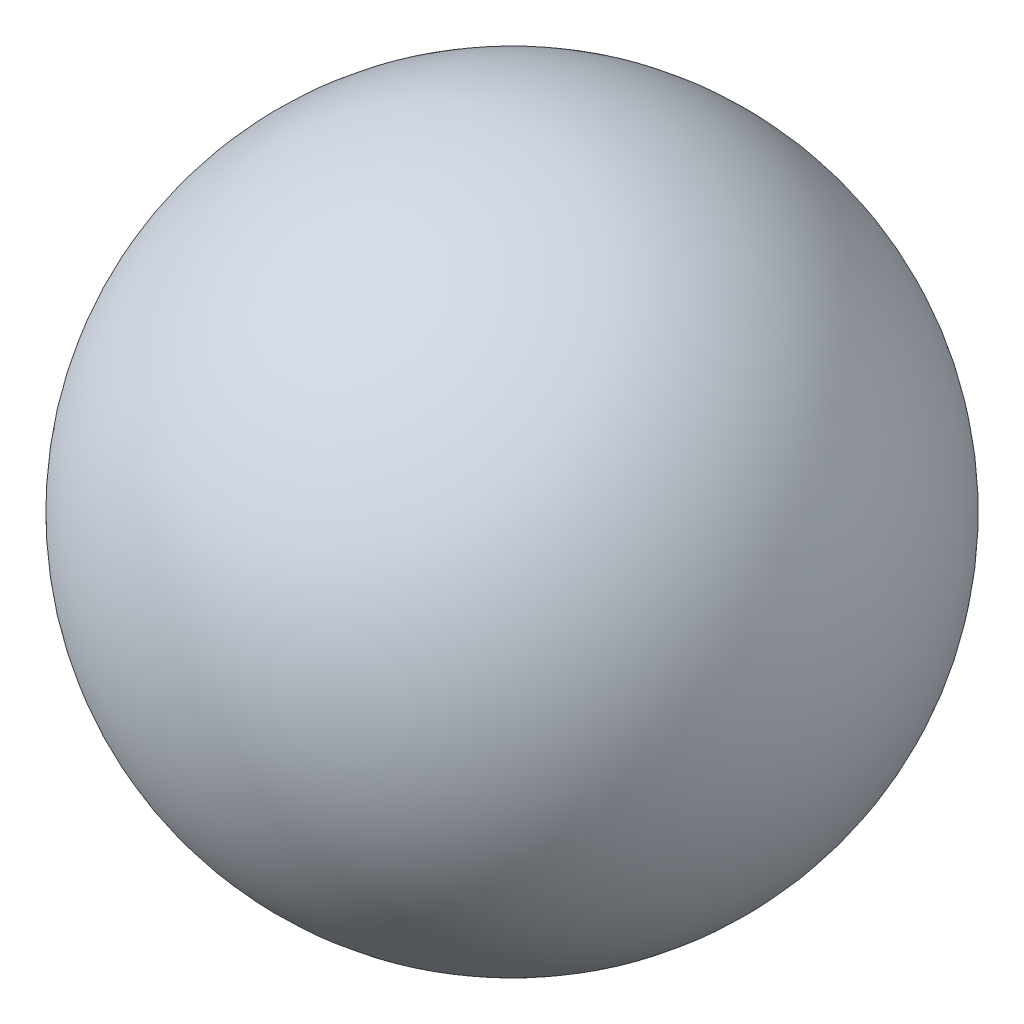
SolidWorks part; units mm, degrees
material "ABS"
ref_plane "Front Plane" through (0, 0, 0) normal (0, 0, 1) x (1, 0, 0)
ref_plane "Top Plane" through (0, 0, 0) normal (0, 1, 0) x (1, 0, 0)
ref_plane "Right Plane" through (0, 0, 0) normal (1, 0, 0) x (0, 0, -1)
sketch "Sketch1" plane through (0, 0, 0) normal (0, 0, 1) x (1, 0, 0)
  line L1 (0, 40) -> (0, 39.458)
  line L2 (0, 0) -> (0, 0.542)
  arc A0 (0, 40) -> (0, 0) centre (0, 20) cw
  arc A1 (0, 39.458) -> (0, 0.542) centre (0, 20) cw
  point P3 (0, 0)
  dimension "D1" = 20
  dimension "D2" = 0.542
revolve "Revolve1" add sketch "Sketch1" angle 360 about L1
